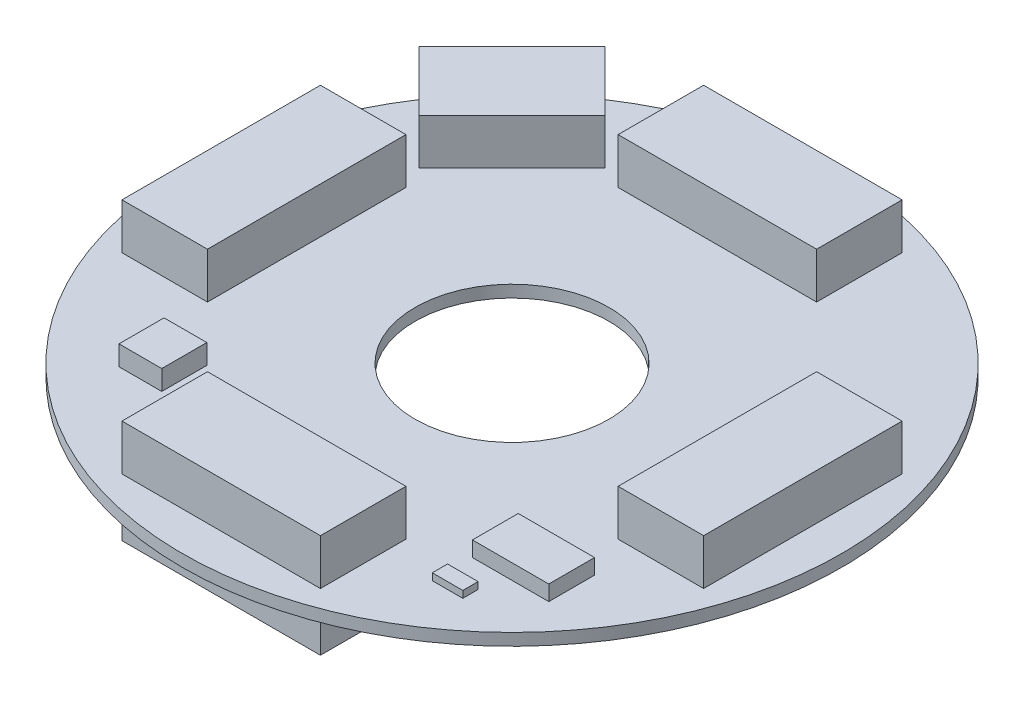
SolidWorks part; units mm, degrees
material "Custom Plastic"
ref_plane "Front Plane" through (0, 0, 0) normal (0, 0, 1) x (1, 0, 0)
ref_plane "Top Plane" through (0, 0, 0) normal (0, 1, 0) x (1, 0, 0)
ref_plane "Right Plane" through (0, 0, 0) normal (1, 0, 0) x (0, 0, -1)
sketch "Sketch1" plane through (0, 0, 0) normal (0, 1, 0) x (1, 0, 0)
  circle A0 centre (0, 0) radius 6.35
  circle A1 centre (0, 0) radius 21.59
  dimension "D1" = 43.18
  dimension "D2" = 12.7
extrude "Boss-Extrude1" add sketch "Sketch1" along normal blind 0.7874
sketch "Sketch2" plane through (0, 0.7874, 0) normal (0, 1, 0) x (1, 0, 0)
  line L0 (0, 0) -> (-13.45, 0) construction
  line L1 (-19.05, 6.5) -> (-13.45, 6.5)
  line L2 (-19.05, 6.5) -> (-19.05, -6.5)
  line L3 (-19.05, -6.5) -> (-13.45, -6.5)
  line L4 (-13.45, 6.5) -> (-13.45, -6.5)
  line L5 (0, 0) -> (-15.2664, 15.2664) construction
  line L6 (0, 0) -> (15.2664, 15.2664) construction
  line L7 (6.5, 19.05) -> (6.5, 13.45)
  line L8 (-6.5, 13.45) -> (6.5, 13.45)
  line L9 (-6.5, 19.05) -> (6.5, 19.05)
  line L10 (-6.5, 19.05) -> (-6.5, 13.45)
  line L11 (-6.5, -19.05) -> (-6.5, -13.45)
  line L12 (6.5, -19.05) -> (-6.5, -19.05)
  line L13 (6.5, -13.45) -> (-6.5, -13.45)
  line L14 (6.5, -19.05) -> (6.5, -13.45)
  line L15 (19.05, 6.5) -> (13.45, 6.5)
  line L16 (13.45, -6.5) -> (13.45, 6.5)
  line L17 (19.05, -6.5) -> (19.05, 6.5)
  line L18 (19.05, -6.5) -> (13.45, -6.5)
  circle A0 centre (0, 0) radius 21.59 construction
  dimension "D1" = 13
  dimension "D2" = 5.6
  dimension "D3" = 19.05
  dimension "D4" = 45
extrude "Face Board Connectors" add sketch "Sketch2" along normal blind 3
sketch "Sketch3" plane through (0, 0, 0) normal (0, -1, 0) x (1, 0, 0)
  line L4 (6.5, 19.05) -> (-6.5, 19.05)
  line L5 (6.5, 13.45) -> (6.5, 19.05)
  line L6 (-6.5, 13.45) -> (6.5, 13.45)
  line L7 (-6.5, 19.05) -> (-6.5, 13.45)
  line L8 (6.5, 19.05) -> (-6.5, 19.05)
  line L9 (6.5, 13.45) -> (6.5, 19.05)
  line L10 (-6.5, 13.45) -> (6.5, 13.45)
  line L11 (-6.5, 19.05) -> (-6.5, 13.45)
  dimension "D1" = 0
extrude "Bottom Face Board Connector" add sketch "Sketch3" along normal blind 3
sketch "Sketch4" plane through (0, 0.7874, 0) normal (0, 1, 0) x (1, 0, 0)
  line L0 (-18.0011, 11.92) -> (-14.1121, 8.0309)
  line L1 (-14.1121, 8.0309) -> (-8.0309, 14.1121)
  line L2 (-8.0309, 14.1121) -> (-11.92, 18.0011)
  line L3 (-11.92, 18.0011) -> (-18.0011, 11.92)
  line L4 (-11.0715, 11.0715) -> (0, 0) construction
  line L5 (0, 0) -> (-21.59, 0) construction
  circle A0 centre (0, 0) radius 21.59 construction
  dimension "D1" = 45
  dimension "D2" = 5.5
  dimension "D3" = 8.6
extrude "Programming Connector" add sketch "Sketch4" along normal blind 3
sketch "Sketch5" plane through (0, 0.7874, 0) normal (0, 1, 0) x (1, 0, 0)
  line L1 (-12.6766, -10.1171) -> (-9.8766, -10.1171)
  line L2 (-12.6766, -10.1171) -> (-12.6766, -13.0671)
  line L3 (-12.6766, -13.0671) -> (-9.8766, -13.0671)
  line L4 (-9.8766, -10.1171) -> (-9.8766, -13.0671)
  dimension "D1" = 2.8
  dimension "D2" = 2.95
extrude "I2C Translator" add sketch "Sketch5" along normal blind 1.3
sketch "Sketch6" plane through (0, 0.7874, 0) normal (0, 1, 0) x (1, 0, 0)
  line L1 (9.72, -9.3144) -> (14.72, -9.3144)
  line L2 (9.72, -9.3144) -> (9.72, -12.3144)
  line L3 (9.72, -12.3144) -> (14.72, -12.3144)
  line L4 (14.72, -9.3144) -> (14.72, -12.3144)
  dimension "D1" = 5
  dimension "D2" = 3
extrude "Accelerometer" add sketch "Sketch6" along normal blind 1
sketch "Sketch7" plane through (0, 0.7874, 0) normal (0, 1, 0) x (1, 0, 0)
  line L0 (9.72, -9.3144) -> (9.72, -12.3144) construction
  line L1 (9.72, -13.9433) -> (11.72, -13.9433)
  line L2 (9.72, -13.9433) -> (9.72, -14.9433)
  line L3 (9.72, -14.9433) -> (11.72, -14.9433)
  line L4 (11.72, -13.9433) -> (11.72, -14.9433)
  dimension "D1" = 2
  dimension "D2" = 1
extrude "Boss-Extrude7" add sketch "Sketch7" along normal blind 0.45
sketch "Sketch8" plane through (0, 0, 0) normal (0, -1, 0) x (1, 0, 0)
  line L0 (-9.845, -16.8454) -> (-2.8446, -9.845)
  line L1 (-2.8446, -9.845) -> (-9.845, -2.8446)
  line L2 (-9.845, -2.8446) -> (-16.8454, -9.845)
  line L3 (-16.8454, -9.845) -> (-9.845, -16.8454)
  line L4 (0, 0) -> (-6.3448, -6.3448) construction
  line L5 (0, 0) -> (-21.59, 0) construction
  circle A0 centre (0, 0) radius 21.59 construction
  dimension "D1" = 45
  dimension "D2" = 9.9
  dimension "D3" = 9.9
extrude "Boss-Extrude8" add sketch "Sketch8" along normal blind 1.2
sketch "Sketch9" plane through (0, 0, 0) normal (0, -1, 0) x (1, 0, 0)
  line L1 (-9.0469, 5.4142) -> (-11.7369, 5.4142)
  line L2 (-9.0469, 5.4142) -> (-9.0469, 11.9142)
  line L3 (-9.0469, 11.9142) -> (-11.7369, 11.9142)
  line L4 (-11.7369, 5.4142) -> (-11.7369, 11.9142)
  dimension "D1" = 6.5
  dimension "D2" = 2.69
extrude "Boss-Extrude9" add sketch "Sketch9" along normal blind 2.69
